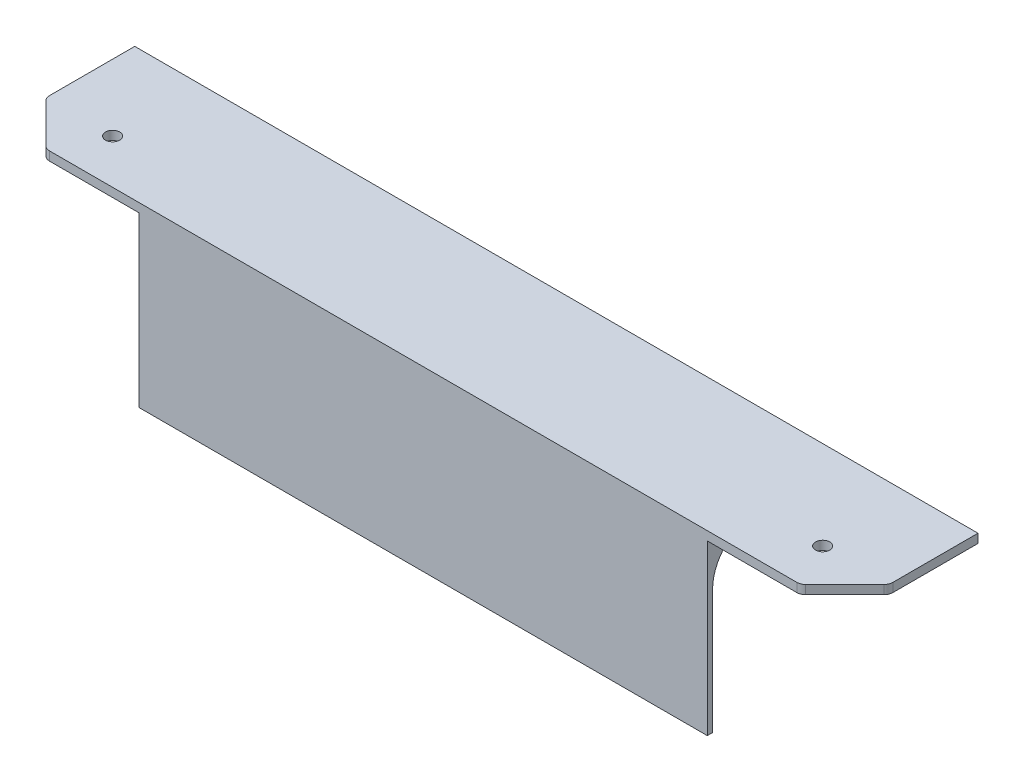
SolidWorks part; units mm, degrees
ref_plane "Plan de face" through (0, 0, 0) normal (0, 0, 1) x (1, 0, 0)
ref_plane "Plan de dessus" through (0, 0, 0) normal (0, 1, 0) x (1, 0, 0)
ref_plane "Plan de droite" through (0, 0, 0) normal (1, 0, 0) x (0, 0, -1)
sketch "Esquisse2" plane through (0, 0, 0) normal (0, 1, 0) x (1, 0, 0)
  line L1 (-95, -15) -> (95, -15)
  line L2 (-95, -15) -> (-95, 15)
  line L3 (-95, 15) -> (95, 15)
  line L4 (95, -15) -> (95, 15)
  line L5 (-95, -15) -> (95, 15) construction
  line L6 (-95, 15) -> (95, -15) construction
  point P0 (0, 0)
  dimension "D1" = 190
  dimension "D2" = 30
extrude "Boss.-Extru.1" add sketch "Esquisse2" along normal blind 2
sketch "Esquisse3" plane through (0, 0, 0) normal (0, -1, 0) x (1, 0, 0)
  line L0 (-95, 15) -> (95, 15) construction
  line L1 (-64, 15) -> (64, 15)
  line L2 (-64, 15) -> (-64, 13.8)
  line L3 (-64, 13.8) -> (64, 13.8)
  line L4 (64, 15) -> (64, 13.8)
  line L5 (0, 0) -> (0, 13.8) construction
  dimension "D1" = 1.2
  dimension "D2" = 128
extrude "Boss.-Extru.2" add sketch "Esquisse3" along normal blind 38
chamfer "Chanfrein1" distance 10 angle 45 2 edges at (95, 1, 15) (-95, 1, 15)
fillet "Congé1" radius 2 4 edges at (-85, 1, 15) (-95, 1, 5) (95, 1, 5) (85, 1, 15)
sketch "Esquisse4" plane through (0, 2, 0) normal (0, 1, 0) x (1, 0, 0)
  line L0 (-95, -5) -> (95, -5) construction
  line L3 (95, -4.1716) -> (95, 15) construction
  line L4 (-95, 15) -> (-95, -4.1716) construction
  line L5 (-84.1716, -15) -> (84.1716, -15) construction
  circle A0 centre (-80, -5) radius 1.6
  circle A1 centre (80, -5) radius 1.6
  dimension "D1" = 3.2
  dimension "D2" = 15
  dimension "D3" = 15
  dimension "D4" = 10
extrude "Enlèv. mat.-Extru.1" cut sketch "Esquisse4" against normal through all
fillet "Congé2" radius 10 1 edges at (0, 0, 13.8)
